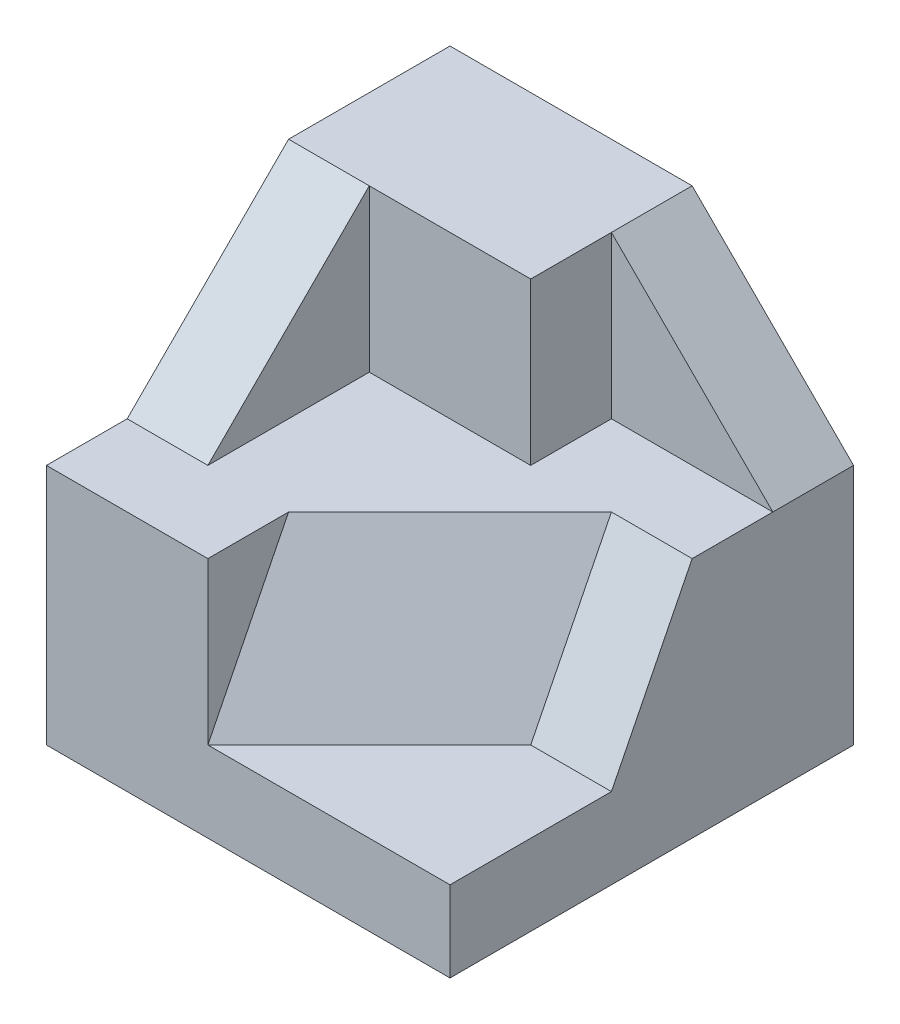
SolidWorks part; units mm, degrees
ref_plane "Front Plane" through (0, 0, 0) normal (0, 0, 1) x (1, 0, 0)
ref_plane "Top Plane" through (0, 0, 0) normal (0, 1, 0) x (1, 0, 0)
ref_plane "Right Plane" through (0, 0, 0) normal (1, 0, 0) x (0, 0, -1)
sketch "Sketch1" plane through (0, 0, 0) normal (0, 0, 1) x (1, 0, 0)
  line L1 (2.5, -2.5) -> (-2.5, -2.5)
  line L2 (2.5, -2.5) -> (2.5, 2.5)
  line L3 (2.5, 2.5) -> (-2.5, 2.5)
  line L4 (-2.5, -2.5) -> (-2.5, 2.5)
  line L5 (2.5, -2.5) -> (-2.5, 2.5) construction
  line L6 (2.5, 2.5) -> (-2.5, -2.5) construction
  point P0 (0, 0)
  dimension "D1" = 5
  dimension "D2" = 5
extrude "Boss-Extrude1" add sketch "Sketch1" along normal blind 5
sketch "Sketch2" plane through (0, 2.5, 0) normal (0, 1, 0) x (1, 0, 0)
  line L0 (-2.5, -5) -> (-0.5, -5)
  line L1 (2.5, -5) -> (-2.5, -5) construction
  line L2 (-0.5, -5) -> (-0.5, -2)
  line L3 (-0.5, -2) -> (-1.5, -2)
  line L4 (-1.5, -2) -> (-1.5, -4)
  line L5 (-1.5, -4) -> (-2.5, -4)
  line L6 (-2.5, -5) -> (-2.5, 0) construction
  line L7 (-2.5, -4) -> (-2.5, -5)
  dimension "D1" = 1
  dimension "D2" = 2
  dimension "D3" = 1
  dimension "D4" = 2
extrude "Cut-Extrude1" cut sketch "Sketch2" against normal blind 2
sketch "Sketch3" plane through (-2.5, 0, 0) normal (-1, 0, 0) x (0, 0, 1)
  line L0 (4, 0.5) -> (2, 2.5)
  line L1 (2, 2.5) -> (4, 2.5)
  line L2 (4, 2.5) -> (4, 0.5)
extrude "Cut-Extrude2" cut sketch "Sketch3" against normal blind 1
sketch "Sketch4" plane through (0, 0, 5) normal (0, 0, 1) x (1, 0, 0)
  line L0 (-0.5, 0.5) -> (2.5, 0.5)
  line L1 (2.5, -2.5) -> (2.5, 2.5) construction
  line L2 (2.5, 0.5) -> (2.5, 2.5)
  line L3 (2.5, 2.5) -> (-0.5, 2.5)
  line L4 (-0.5, 2.5) -> (-0.5, 0.5)
extrude "Cut-Extrude3" cut sketch "Sketch4" against normal blind 3
sketch "Sketch5" plane through (0, 0, 2) normal (0, 0, 1) x (1, 0, 0)
  line L0 (2.5, 2.5) -> (2.5, 0.5)
  line L1 (2.5, 0.5) -> (0.5, 0.5)
  line L2 (2.5, 0.5) -> (-1.5, 0.5) construction
  line L3 (0.5, 0.5) -> (0.5, 2.5)
  line L4 (2.5, 2.5) -> (-1.5, 2.5) construction
  line L5 (0.5, 2.5) -> (2.5, 2.5)
  dimension "D1" = 2
extrude "Cut-Extrude4" cut sketch "Sketch5" against normal blind 1
sketch "Sketch6" plane through (0, 0, 1) normal (0, 0, 1) x (1, 0, 0)
  line L0 (2.5, 0.5) -> (0.5, 2.5)
  line L1 (0.5, 2.5) -> (2.5, 2.5)
  line L2 (2.5, 2.5) -> (2.5, 0.5)
extrude "Cut-Extrude5" cut sketch "Sketch6" against normal blind 1
sketch "Sketch7" plane through (0, 0.5, 0) normal (0, 1, 0) x (1, 0, 0)
  line L0 (2.5, -5) -> (2.5, -3)
  line L1 (2.5, -1) -> (2.5, -5) construction
  line L2 (2.5, -3) -> (1.5, -3)
  line L3 (1.5, -3) -> (-0.5, -5)
  line L4 (-2.5, -5) -> (2.5, -5) construction
  line L5 (-0.5, -5) -> (2.5, -5)
  dimension "D1" = 2
  dimension "D2" = 3
  dimension "D3" = 1
extrude "Cut-Extrude6" cut sketch "Sketch7" against normal blind 2
sketch "Sketch8" plane through (2.5, 0, 0) normal (1, 0, 0) x (0, 0, -1)
  line L0 (-3, -1.5) -> (-2, 0.5)
  line L1 (-1, 0.5) -> (-2, 0.5) construction
  line L2 (-2, 0.5) -> (-3, 0.5)
  line L3 (-2, 0.5) -> (-4, 0.5) construction
  line L4 (-3, 0.5) -> (-3, -1.5)
  dimension "D1" = 2
extrude "Cut-Extrude7" cut sketch "Sketch8" against normal blind 1
sketch "Sketch9" plane through (2.5, 0, 0) normal (1, 0, 0) x (0, 0, -1)
  line L0 (-5, -1.5) -> (-4, 0.5)
  line L1 (-3, 0.5) -> (-5, 0.5) construction
  line L2 (-4, 0.5) -> (-5, 0.5)
  line L3 (-5, 0.5) -> (-5, -1.5)
  dimension "D1" = 1
extrude "Cut-Extrude8" cut sketch "Sketch9" against normal blind 3
sketch "Sketch10" plane through (0, 0.5, 0) normal (0, 1, 0) x (1, 0, 0)
  line L0 (-0.5, -4) -> (1.5, -2)
ref_plane "Plane1" through (1.6667, 0.8333, 1.6667) normal (-0.6667, -0.3333, -0.6667) x (-0.7454, 0.2981, 0.5963)
sketch "Sketch11" plane through (1.6667, 0.8333, 1.6667) normal (-0.6667, -0.3333, -0.6667) x (-0.7454, 0.2981, 0.5963)
  line L0 (2.9069, -1.3416) -> (0.2236, -0.4472)
  line L1 (0.2236, -0.4472) -> (0.2236, -2.6833)
  line L2 (0.2236, -2.6833) -> (2.9069, -3.5777)
  line L3 (2.9069, -3.5777) -> (2.9069, -1.3416)
extrude "Cut-Extrude9" cut sketch "Sketch11" against normal blind 3
